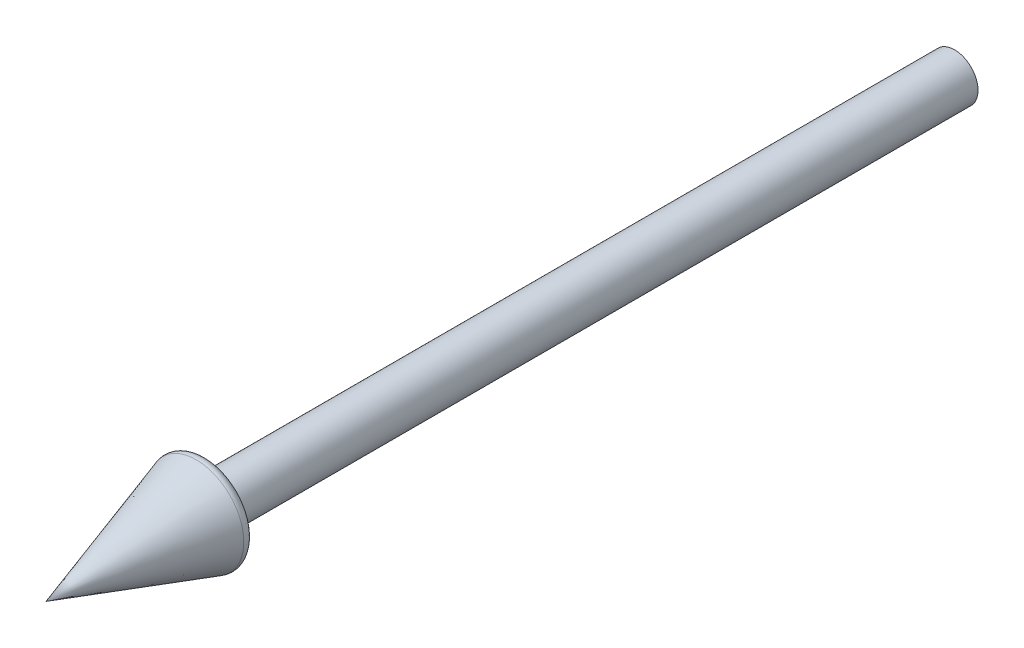
SolidWorks part; units mm, degrees
ref_plane "Front Plane" through (0, 0, 0) normal (0, 0, 1) x (1, 0, 0)
ref_plane "Top Plane" through (0, 0, 0) normal (0, 1, 0) x (1, 0, 0)
ref_plane "Right Plane" through (0, 0, 0) normal (1, 0, 0) x (0, 0, -1)
sketch "Sketch1" plane through (0, 0, 0) normal (0, 1, 0) x (1, 0, 0)
  line L0 (0, 0) -> (0, -1219.1809)
  line L1 (0, -1219.1809) -> (63.7176, -1017.4796)
  line L2 (54.182, -1004.4673) -> (31.4559, -1004.4673)
  line L3 (31.4559, -1004.4673) -> (31.4559, 0)
  line L4 (31.4559, 0) -> (0, 0)
  arc A0 (63.7176, -1017.4796) -> (54.182, -1004.4673) centre (54.182, -1014.4673) ccw
  dimension "D1" = 10
revolve "Revolve1" add sketch "Sketch1" angle 360 about L0
